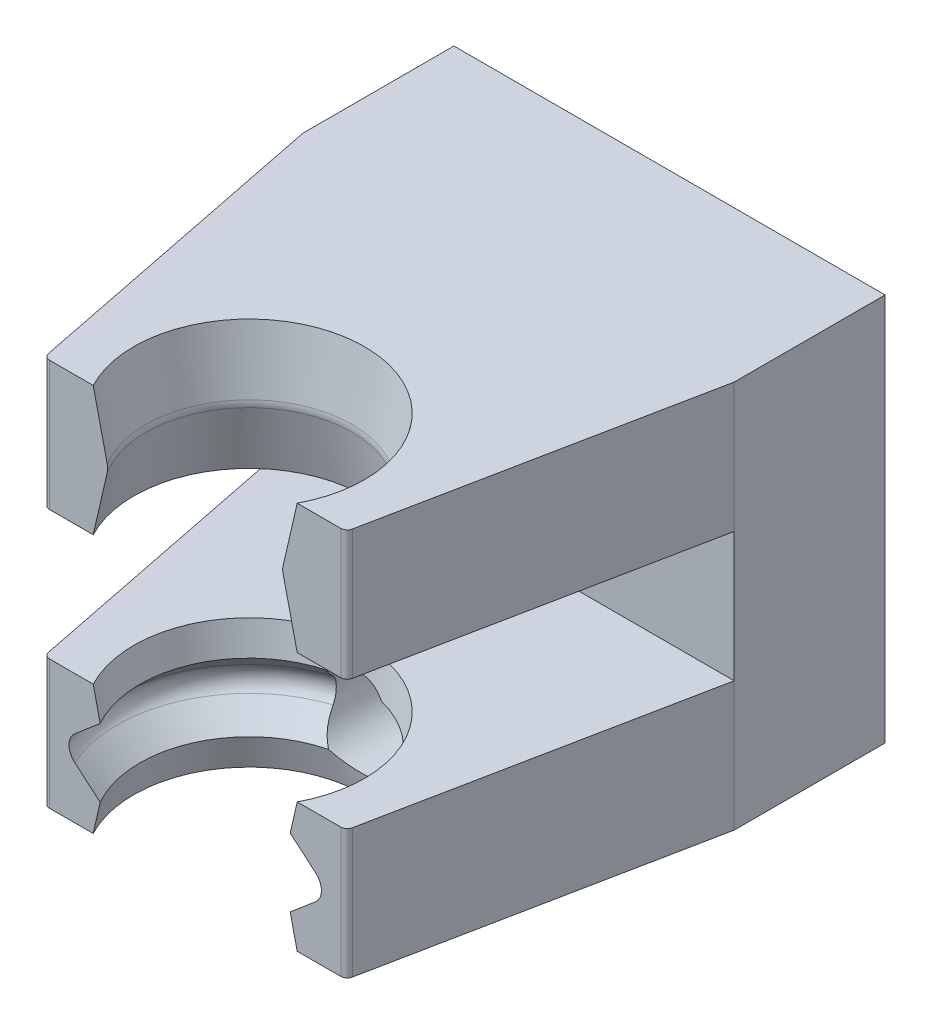
SolidWorks part; units mm, degrees
ref_plane "Front Plane" through (0, 0, 0) normal (0, 0, 1) x (1, 0, 0)
ref_plane "Top Plane" through (0, 0, 0) normal (0, 1, 0) x (1, 0, 0)
ref_plane "Right Plane" through (0, 0, 0) normal (1, 0, 0) x (0, 0, -1)
sketch "Sketch1" plane through (0, 0, 0) normal (0, 0, 1) x (1, 0, 0)
  line L1 (-10, -9) -> (10, -9)
  line L2 (-10, -9) -> (-10, 9)
  line L3 (-10, 9) -> (10, 9)
  line L4 (10, -9) -> (10, 9)
  line L5 (-10, -9) -> (10, 9) construction
  line L6 (-10, 9) -> (10, -9) construction
  point P0 (0, 0)
  dimension "D1" = 18
  dimension "D2" = 20
extrude "Boss-Extrude1" add sketch "Sketch1" along normal blind 7
sketch "Sketch2" plane through (0, 0, 7) normal (0, 0, 1) x (1, 0, 0)
  line L0 (-10, 9) -> (-10, -9) construction
  line L1 (10, -9) -> (-10, -9)
  line L2 (10, -9) -> (10, -3)
  line L3 (10, -3) -> (-10, -3)
  line L4 (-10, -9) -> (-10, -3)
  line L5 (10, -9) -> (10, 9) construction
  line L6 (-10, 9) -> (10, 9)
  line L7 (-10, 9) -> (-10, 3)
  line L8 (-10, 3) -> (10, 3)
  line L9 (10, 9) -> (10, 3)
  dimension "D1" = 6
  dimension "D2" = 6
extrude "Boss-Extrude2" add sketch "Sketch2" along normal blind 15
sketch "Sketch3" plane through (0, -9, 0) normal (0, -1, 0) x (1, 0, 0)
  line L0 (-10, 7) -> (10, 7) construction
  line L1 (-10, 7) -> (10, 7) construction
  line L2 (0, 22) -> (0, 19.5) construction
  line L3 (-10, 22) -> (10, 22) construction
  line L4 (-7, 22) -> (7, 22) construction
  line L5 (-7, 22) -> (-10, 7)
  line L6 (-10, 7) -> (-10, 22)
  line L7 (-10, 22) -> (-7, 22)
  line L8 (7, 22) -> (10, 22)
  line L9 (10, 22) -> (10, 7)
  line L10 (10, 7) -> (7, 22)
  circle A0 centre (0, 19.5) radius 5.35
  point P9 (5.4429, 17)
  point P15 (0, 22)
  dimension "D1" = 10.7
  dimension "D2" = 2.5
  dimension "D3" = 3
extrude "Cut-Extrude1" cut sketch "Sketch3" against normal up to surface (18 mm away) up to face at (0, 9, 11)
ref_axis "Axis1" through (0, -3, 19.5) along (0, -1, 0)
ref_plane "Plane1" through (0, 0, 19.5) normal (0, 0, 1) x (1, 0, 0)
sketch "Sketch4" plane through (0, 0, 19.5) normal (0, 0, 1) x (1, 0, 0)
  line L0 (-5.35, -3) -> (-5.35, -9)
  line L1 (5.35, -9) -> (5.35, -3)
  line L2 (5.35, -9) -> (5.35, -3)
  line L3 (-5.35, -3) -> (-5.35, -9)
  line L4 (-5.35, -3) -> (-4.7814, -5.8431)
  line L5 (-4.7814, -6.1569) -> (-5.35, -9)
  line L6 (-4.75, -6) -> (-5.35, -6) construction
  line L7 (5.35, -9) -> (5.35, -3)
  line L8 (-5.35, -3) -> (-5.35, -9)
  arc A0 (-4.7814, -5.8431) -> (-4.7814, -6.1569) centre (-5.5658, -6) cw
  dimension "D1" = 0.8
  dimension "D2" = 0.6
revolve "Revolve4" add sketch "Sketch4" angle 360 about axis through (0, -3, 19.5) along (0, -1, 0)
sketch "Sketch5" plane through (0, 0, 22) normal (0, 0, 1) x (1, 0, 0)
  line L1 (-7, -9) -> (7, -9)
  line L2 (-7, -9) -> (-7, -3)
  line L3 (-7, -3) -> (7, -3)
  line L4 (7, -9) -> (7, -3)
extrude "Cut-Extrude2" cut sketch "Sketch5" along normal through all
fillet "Fillet1" radius 0.3 6 edges at (7, 6, 22) (-4.73, 6, 22) (4.73, 6, 22) (-7, 6, 22) (-7, -6, 22) (7, -6, 22)
sketch "Sketch6" plane through (0, 0, 7) normal (0, 0, 1) x (1, 0, 0)
  line L0 (-10, 3) -> (-10, -3) construction
  line L1 (-10, 0) -> (10, 0)
  line L2 (-10, 0) -> (-10, 9)
  line L3 (-10, 9) -> (10, 9)
  line L4 (10, 0) -> (10, 9)
extrude "Cut-Extrude3" cut sketch "Sketch6" against normal through all both and the other way through all
mirror "Mirror2" about plane through (-10, 0, 0) normal (0, -1, 0) of bodies 106
sketch "Sketch7" plane through (0, 0, 0) normal (0, 0, -1) x (-1, 0, 0)
  line L0 (-10, -3) -> (10, -3) construction
  line L1 (-10, -3) -> (10, -3) construction
  line L2 (0, -3) -> (0, -9) construction
  line L3 (10, -9) -> (-10, -9) construction
  circle A0 centre (0, -6) radius 2
  dimension "D1" = 4
extrude "Cut-Extrude4" cut sketch "Sketch7" against normal through all both and the other way through all
sketch "Sketch8" plane through (0, 0, 19.5) normal (0, 0, 1) x (1, 0, 0)
  line L0 (-4.7814, -6.1569) -> (-5.35, -9)
  line L1 (5.35, -9) -> (4.7814, -6.1569)
  line L2 (5.35, -9) -> (4.7814, -6.1569)
  line L3 (-4.7814, -6.1569) -> (-5.35, -9) construction
  line L4 (4.7814, -5.8431) -> (5.35, -3)
  line L5 (-5.35, -3) -> (-4.7814, -5.8431)
  line L6 (-5.35, -3) -> (-4.7814, -5.8431) construction
  line L7 (4.7814, -5.8431) -> (5.35, -3)
  line L8 (-6.1168, -5.42) -> (-5.0657, -4.4216)
  line L9 (-6.1168, -6.58) -> (-5.0657, -7.5784)
  line L10 (-5.0657, -4.4216) -> (-4.7814, -5.8431)
  line L11 (-4.7814, -6.1569) -> (-5.0657, -7.5784)
  arc A0 (-4.7814, -6.1569) -> (-4.7814, -5.8431) centre (-5.5658, -6) ccw
  arc A1 (-4.7814, -6.1569) -> (-4.7814, -5.8431) centre (-5.5658, -6) ccw
  circle A2 centre (-5.5658, -6) radius 0.8
  point P16 (-5.0657, -4.4216)
revolve "Cut-Revolve1" cut sketch "Sketch8" angle 360 about axis through (0, -3, 19.5) along (0, -1, 0)
